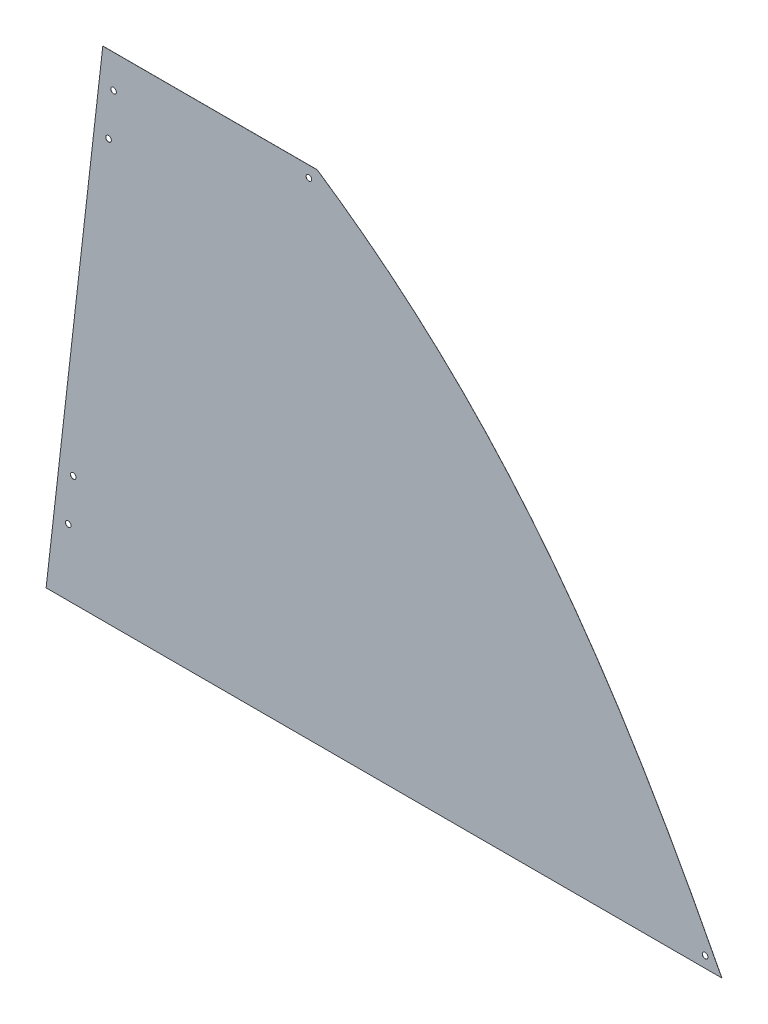
SolidWorks part; units mm, degrees
material "PC High Viscosity"
ref_plane "Front Plane" through (0, 0, 0) normal (0, 0, 1) x (1, 0, 0)
ref_plane "Top Plane" through (0, 0, 0) normal (0, 1, 0) x (1, 0, 0)
ref_plane "Right Plane" through (0, 0, 0) normal (1, 0, 0) x (0, 0, -1)
sketch "Sketch1" plane through (0, 0, 0) normal (0, 0, 1) x (1, 0, 0)
  line L0 (0, 0) -> (739.14, 0)
  line L1 (0, 0) -> (64.6956, 567.8263)
  line L2 (64.6956, 567.8263) -> (277.4206, 567.8263)
  spline S0 degree 3 poles (277.4206, 567.8263) (496.8592, 420.2971) (620.7582, 229.5902) (739.14, 0) knots 0 0 0 0 1 1 1 1
  dimension "D1" = 571.5
  dimension "D2" = 212.725
  dimension "D3" = 739.14
  dimension "D4" = 83.5
extrude "Boss-Extrude1" add sketch "Sketch1" along normal blind 0.127
sketch "Sketch2" plane through (0, 0, 0) normal (0, 0, -1) x (-1, 0, 0)
  line L0 (-295.925, 555.1263) -> (-63.2487, 555.1263) construction
  line L1 (-64.6956, 567.8263) -> (0, 0) construction
  line L2 (-277.4206, 567.8263) -> (-64.6956, 567.8263) construction
  line L3 (-732.5648, 12.7) -> (-1.447, 12.7) construction
  line L4 (0, 0) -> (-739.14, 0) construction
  spline S0 degree 3 poles (-739.14, 0) (-620.7582, 229.5902) (-496.8592, 420.2971) (-277.4206, 567.8263) knots 0 0 0 0 1 1 1 1 construction
  point P6 (-261, 555.1263)
  point P7 (-80.3937, 555.1263)
  point P14 (-707.1648, 12.7)
  point P15 (-26.847, 12.7)
  dimension "D1" = 12.7
  dimension "D2" = 17.145
  dimension "D3" = 34.925
  dimension "D4" = 12.7
  dimension "D5" = 25.4
  dimension "D6" = 25.4
hole_wizard "1/4 (0.25) Diameter Hole1" positions "Sketch3" profile "Sketch4" hole size "1/4" standard "ANSI Inch"
sketch "Sketch3" plane through (0, 0, 0) normal (0, 0, -1) x (-1, 0, 0)
  point P0 (-258.101, 541.9348)
  point P3 (-83.6862, 541.9348)
  point P7 (-704.6174, 12.7)
  point P10 (-26.9594, 12.7)
sketch "Sketch4" plane through (258.101, 541.9348, 0) normal (1, 0, 0) x (0, 1, 0)
  line L0 (0, 0) -> (0, 6.35)
  line L1 (0, 6.35) -> (3.175, 6.35)
  line L2 (3.175, 6.35) -> (3.175, 0)
  line L5 (3.175, 0) -> (0, 0)
  line L11 (0, -6.35) -> (0, 107.95) construction
  dimension "Thru Hole Dia." = 6.35
  dimension "Thru Hole Depth" = 6.35
sketch "Sketch5" plane through (0, 0, 0) normal (0, 0, -1) x (-1, 0, 0)
  line L0 (-64.6956, 567.8263) -> (-32.7402, 567.8263)
  line L1 (-32.7402, 567.8263) -> (31.9554, 0)
  line L2 (31.9554, 0) -> (0, 0)
  line L3 (-64.6956, 567.8263) -> (0, 0) construction
  line L4 (-64.6956, 567.8263) -> (0, 0)
  dimension "D1" = 31.75
extrude "Boss-Extrude2" add sketch "Sketch5" against normal up to surface (0.127 mm away) up to face at (328.029, 212.9349, 0.127)
sketch "Sketch6" plane through (0, 0, 0.127) normal (0, 0, 1) x (1, 0, 0)
  line L0 (49.357, 567.8263) -> (-15.3386, 0) construction
  line L1 (277.4206, 567.8263) -> (32.7402, 567.8263) construction
  line L2 (-31.9554, 0) -> (739.14, 0) construction
  line L3 (-31.9554, 0) -> (32.7402, 567.8263) construction
  point P8 (45.044, 529.9712)
  point P9 (39.2933, 479.4978)
  point P10 (-6.7125, 75.7102)
  point P11 (-0.9618, 126.1836)
  dimension "D1" = 16.51
  dimension "D2" = 50.8
  dimension "D3" = 38.1
  dimension "D4" = 50.8
  dimension "D5" = 76.2
hole_wizard "1/4 (0.25) Diameter Hole2" positions "Sketch7" profile "Sketch8" hole size "1/4" standard "ANSI Inch"
sketch "Sketch7" plane through (0, 0, 0.127) normal (0, 0, 1) x (1, 0, 0)
  point P0 (-6.7125, 75.7102)
  point P3 (-0.9618, 126.1836)
  point P6 (39.2933, 479.4978)
  point P9 (45.044, 529.9712)
sketch "Sketch8" plane through (-6.7125, 75.7102, 0.127) normal (1, 0, 0) x (0, -1, 0)
  line L0 (0, 0) -> (0, 2.0337)
  line L1 (0, 2.0337) -> (3.175, 0.126)
  line L2 (3.175, 0.126) -> (3.175, 0)
  line L5 (3.175, 0) -> (0, 0)
  line L10 (0, 2.0337) -> (-3.175, 0.126) construction
  line L11 (0, -6.35) -> (0, 107.95) construction
  dimension "Hole Dia." = 6.35
  dimension "Hole Depth" = 0.126
  dimension "Drill Angle" = 118
sketch "Sketch9" plane through (0, 0, 0.127) normal (0, 0, 1) x (1, 0, 0)
  line L0 (-31.9554, 0) -> (739.14, 0) construction
  line L1 (277.4206, 567.8263) -> (32.7402, 567.8263) construction
  point P0 (720.09, 12.7)
  point P4 (267.8956, 555.1263)
  dimension "D1" = 12.7
  dimension "D2" = 19.05
  dimension "D3" = 12.7
  dimension "D4" = 9.525
hole_wizard "1/4 (0.25) Diameter Hole3" positions "Sketch10" profile "Sketch12" hole size "1/4" standard "ANSI Inch" end condition up to next
sketch "Sketch10" plane through (0, 0, 0.127) normal (0, 0, 1) x (1, 0, 0)
  point P0 (720.09, 12.7)
  point P4 (267.8956, 555.1263)
sketch "Sketch12" plane through (720.09, 12.7, 0.127) normal (1, 0, 0) x (0, -1, 0)
  line L0 (0, 0) -> (0, 0.127)
  line L1 (0, 0.127) -> (3.175, 0.127)
  line L2 (3.175, 0.127) -> (3.175, 0)
  line L5 (3.175, 0) -> (0, 0)
  line L11 (0, -6.35) -> (0, 107.95) construction
  dimension "Thru Hole Dia." = 6.35
  dimension "Thru Hole Depth" = 0.127
